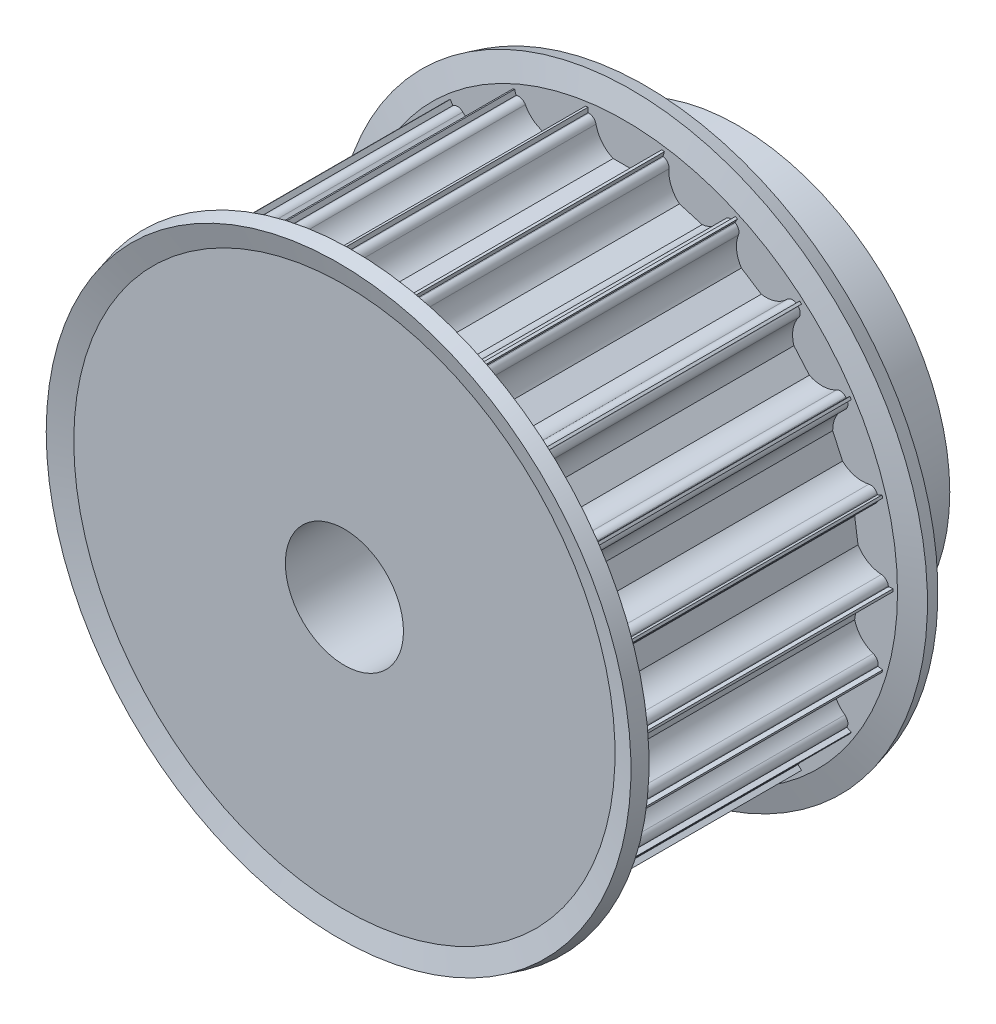
SolidWorks part; units mm, degrees
ref_plane "Front Plane" through (0, 0, 0) normal (0, 0, 1) x (1, 0, 0)
ref_plane "Top Plane" through (0, 0, 0) normal (0, 1, 0) x (1, 0, 0)
ref_plane "Right Plane" through (0, 0, 0) normal (1, 0, 0) x (0, 0, -1)
sketch "Sketch1" plane through (0, 0, 0) normal (1, 0, 0) x (0, 0, -1)
  line L0 (0, 0) -> (51.162, 0) construction
  line L1 (0, 6) -> (0, 27.25)
  line L2 (0, 27.25) -> (30, 27.25)
  line L3 (30, 27.25) -> (30, 21.5)
  line L4 (30, 21.5) -> (40, 21.5)
  line L5 (40, 21.5) -> (40, 6)
  line L6 (40, 6) -> (0, 6)
  point P7 (0, 0)
  dimension "D1" = 27.25
  dimension "D2" = 30
  dimension "D3" = 6
  dimension "D4" = 10
  dimension "D5" = 15.5
revolve "Revolve1" add sketch "Sketch1" angle 360 about L0
sketch "Sketch2" plane through (0, 0, 0) normal (0, 0, 1) x (1, 0, 0)
  line L5 (-3.6742, 26.5) -> (-3.75, 26.5)
  line L6 (-3.75, 26.5) -> (-3.75, 28.5)
  line L7 (-3.75, 28.5) -> (3.75, 28.5)
  line L8 (3.75, 28.5) -> (3.75, 26.5)
  line L9 (3.75, 26.5) -> (3.6742, 26.5)
  line L10 (-1.199, 23.75) -> (1.199, 23.75)
  arc A1 (-2.9394, 25.9) -> (-1.199, 23.75) centre (0, 26.5) ccw
  arc A2 (-2.9394, 25.9) -> (-3.6742, 26.5) centre (-3.6742, 25.75) ccw
  arc A3 (2.9394, 25.9) -> (3.6742, 26.5) centre (3.6742, 25.75) cw
  arc A4 (1.199, 23.75) -> (2.9394, 25.9) centre (0, 26.5) ccw
  point P9 (0, 28.5)
  point P13 (-3, 26.5)
  point P16 (3, 26.5)
  dimension "D1" = 3
  dimension "D2" = 26.5
  dimension "D4" = 0.75
  dimension "D5" = 0.75
  dimension "D7" = 2.75
  dimension "D3" = 7.5
  dimension "D6" = 2
extrude "Cut-Extrude1" cut sketch "Sketch2" against normal up to next (30 mm away)
pattern_circular "CirPattern1" count 22 over 360 about axis through (0, 0, 0) along (0, 0, 1) of "Cut-Extrude1"
sketch "Sketch3" plane through (0, 0, 0) normal (1, 0, 0) x (0, 0, -1)
  line L0 (15, 26.9539) -> (15, 6.5954) construction
  line L1 (30, 26.9539) -> (0, 26.9539) construction
  line L2 (30, 6.5954) -> (0, 6.5954) construction
  line L3 (30, 21.5) -> (30, 27.4925)
  line L4 (30, 27.4925) -> (30.592, 29.7018)
  line L5 (30.592, 29.7018) -> (29.1431, 30.09)
  line L6 (29.1431, 30.09) -> (28.5, 27.69)
  line L7 (28.5, 27.69) -> (28.5, 21.5)
  line L8 (28.5, 21.5) -> (30, 21.5)
  line L9 (40, 21.5) -> (30, 21.5) construction
  line L10 (1.5, 27.69) -> (1.5, 21.5)
  line L11 (0.8569, 30.09) -> (1.5, 27.69)
  line L12 (-0.592, 29.7018) -> (0.8569, 30.09)
  line L13 (0, 27.4925) -> (-0.592, 29.7018)
  line L14 (0, 21.5) -> (0, 27.4925)
  line L15 (1.5, 21.5) -> (0, 21.5)
  line L16 (0, 0) -> (-8.7217, 0) construction
  dimension "D1" = 15
  dimension "D2" = 1.5
  dimension "D3" = 6.19
  dimension "D4" = 2.4
revolve "Revolve2" add sketch "Sketch3" angle 360 about L16
